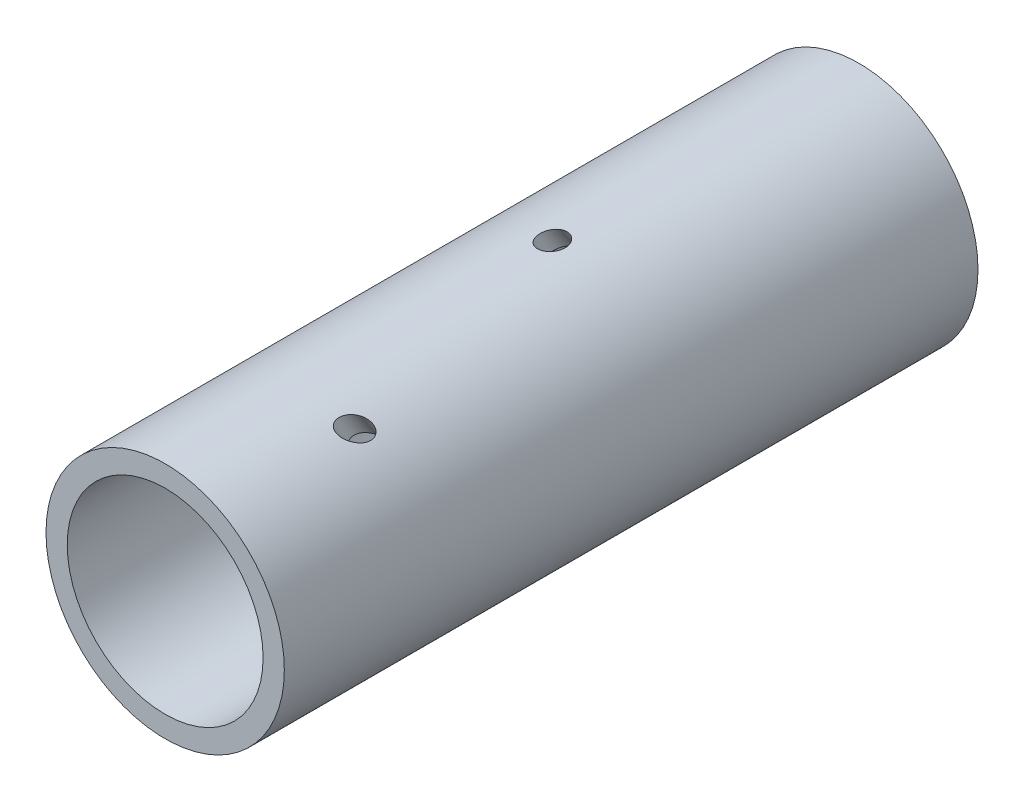
SolidWorks part; units mm, degrees
ref_plane "Ebene vorne" through (0, 0, 0) normal (0, 0, 1) x (1, 0, 0)
ref_plane "Ebene oben" through (0, 0, 0) normal (0, 1, 0) x (1, 0, 0)
ref_plane "Ebene rechts" through (0, 0, 0) normal (1, 0, 0) x (0, 0, -1)
sketch "Skizze1" plane through (0, 0, 0) normal (0, 0, 1) x (1, 0, 0)
  circle A0 centre (0, 0) radius 27.4847
  circle A1 centre (0, 0) radius 22.5874
extrude "Aufsatz-Linear austragen1" add sketch "Skizze1" against normal blind 160
sketch "Skizze2" plane through (0, 0, 0) normal (0, 1, 0) x (1, 0, 0)
  line L0 (-31.2736, 107.1185) -> (40.636, 107.1185)
ref_plane "Ebene1" through (0, -48.9288, -31.7747) normal (0, 0.8387, 0.5446) x (1, 0, 0)
sketch "Skizze5" plane through (0, -48.9288, -31.7747) normal (0, 0.8387, 0.5446) x (1, 0, 0)
  line L3 (0, 134.1873) -> (0, 0) construction
  line L4 (-31.2736, 89.8371) -> (40.636, 89.8371) construction
  point P0 (0, 89.8371)
hole_wizard "Ø6.0 (6) Durchmesser Bohrung2" positions "Skizze7" profile "Skizze6" hole size "Ø6.0" standard "Ansi Metrisch"
sketch "Skizze7" plane through (0, -48.9288, -31.7747) normal (0, 0.8387, 0.5446) x (1, 0, 0)
  point P0 (0, 89.8371)
sketch "Skizze6" plane through (0, 0, -107.1185) normal (1, 0, 0) x (0, 0.5446, -0.8387)
  line L0 (0, 0) -> (0, 83.1134)
  line L1 (0, 83.1134) -> (2.865, 81.3919)
  line L2 (2.865, 81.3919) -> (2.865, 0)
  line L5 (2.865, 0) -> (0, 0)
  line L10 (0, 83.1134) -> (-2.865, 81.3919) construction
  line L11 (0, -6.35) -> (0, 107.95) construction
  dimension "Bohrerdurchmesser" = 5.73
  dimension "Bohrungstiefe" = 81.3919
  dimension "Spitzenwinkel" = 118
ref_plane "Ebene2" through (0, -23.7687, -15.4356) normal (0, 0.8387, 0.5446) x (1, 0, 0)
hole_wizard "Ø6.0 (6) Durchmesser Bohrung3" positions "Skizze10" profile "Skizze9" hole size "Ø6.0" standard "Ansi Metrisch"
sketch "Skizze10" plane through (0, -23.7687, -15.4356) normal (0, 0.8387, 0.5446) x (1, 0, 0)
  ellipse E0 centre (0, 0) end of major axis (-27.4847, 0) minor radius 14.9692 construction
  point P0 (12, 40)
  dimension "D1" = 40
  dimension "D2" = 12
sketch "Skizze9" plane through (12, -1.9831, -48.9824) normal (1, 0, 0) x (0, 0.5446, -0.8387)
  line L0 (0, 0) -> (0, 53.0593)
  line L1 (0, 53.0593) -> (2.775, 51.3919)
  line L2 (2.775, 51.3919) -> (2.775, 0)
  line L5 (2.775, 0) -> (0, 0)
  line L10 (0, 53.0593) -> (-2.775, 51.3919) construction
  line L11 (0, -6.35) -> (0, 107.95) construction
  dimension "Bohrerdurchmesser" = 5.55
  dimension "Bohrungstiefe" = 51.3919
  dimension "Spitzenwinkel" = 118
